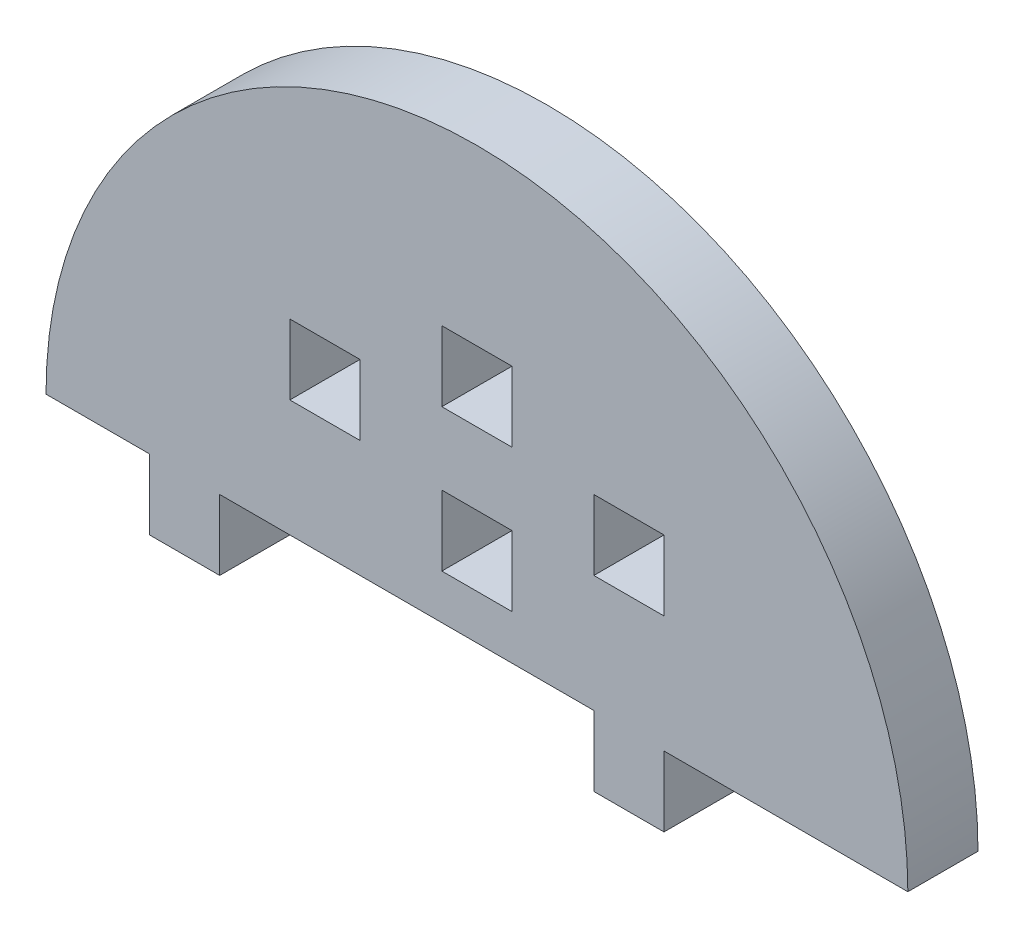
SolidWorks part; units mm, degrees
ref_plane "Front Plane" through (0, 0, 0) normal (0, 0, 1) x (1, 0, 0)
ref_plane "Top Plane" through (0, 0, 0) normal (0, 1, 0) x (1, 0, 0)
ref_plane "Right Plane" through (0, 0, 0) normal (1, 0, 0) x (0, 0, -1)
sketch "Model" plane through (0, 0, 0) normal (0, 0, 1) x (1, 0, 0)
  line L0 (3428.7441, 1203.6605) -> (3428.7441, 1197.6605)
  line L1 (3428.7441, 1197.6605) -> (3434.7441, 1197.6605)
  line L2 (3434.7441, 1197.6605) -> (3434.7441, 1203.6605)
  line L3 (3428.7441, 1219.6605) -> (3434.7441, 1219.6605)
  line L4 (3434.7441, 1219.6605) -> (3434.7441, 1213.6605)
  line L5 (3434.7441, 1213.6605) -> (3428.7441, 1213.6605)
  line L6 (3428.7441, 1213.6605) -> (3428.7441, 1219.6605)
  line L7 (3408.7441, 1219.6605) -> (3402.7441, 1219.6605)
  line L8 (3402.7441, 1219.6605) -> (3402.7441, 1213.6605)
  line L9 (3402.7441, 1213.6605) -> (3408.7441, 1213.6605)
  line L10 (3408.7441, 1213.6605) -> (3408.7441, 1219.6605)
  line L11 (3415.7441, 1225.6605) -> (3421.7441, 1225.6605)
  line L12 (3421.7441, 1225.6605) -> (3421.7441, 1219.6605)
  line L13 (3421.7441, 1219.6605) -> (3415.7441, 1219.6605)
  line L14 (3415.7441, 1219.6605) -> (3415.7441, 1225.6605)
  line L15 (3415.7441, 1207.485) -> (3421.7441, 1207.485)
  line L16 (3421.7441, 1207.485) -> (3421.7441, 1213.485)
  line L17 (3421.7441, 1213.485) -> (3415.7441, 1213.485)
  line L18 (3415.7441, 1213.485) -> (3415.7441, 1207.485)
  line L19 (3396.7441, 1203.6605) -> (3396.7441, 1197.6605)
  line L20 (3396.7441, 1197.6605) -> (3390.7441, 1197.6605)
  line L21 (3390.7441, 1197.6605) -> (3390.7441, 1203.6605)
  line L22 (3390.7441, 1203.6605) -> (3381.887, 1203.6605)
  line L23 (3396.7441, 1203.6605) -> (3428.7441, 1203.6605)
  line L24 (3434.7441, 1203.6605) -> (3455.6012, 1203.6605)
  arc A0 (3455.6012, 1203.6605) -> (3381.887, 1203.6605) centre (3418.7441, 1203.6605) ccw
extrude "Boss-Extrude1" add sketch "Model" along normal blind 6 contours L9 L10 L7 L8 | L14 L13 L12 L11 | L17 L18 L15 L16 | L6 L5 L4 L3 | A0 L22 L21 L20 L19 L23 L0 L1 L2 L24
